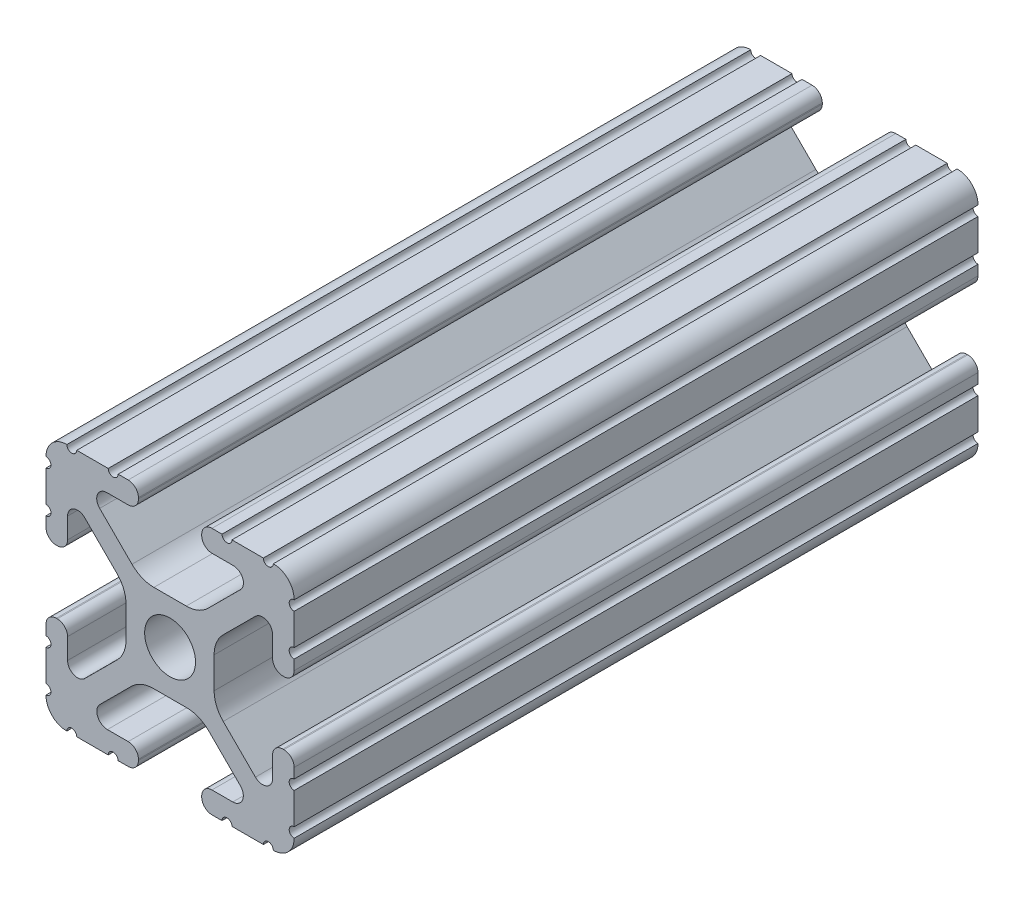
SolidWorks part; units mm, degrees
ref_plane "Front Plane" through (0, 0, 0) normal (0, 0, 1) x (1, 0, 0)
ref_plane "Top Plane" through (0, 0, 0) normal (0, 1, 0) x (1, 0, 0)
ref_plane "Right Plane" through (0, 0, 0) normal (1, 0, 0) x (0, 0, -1)
sketch "Sketch1" plane through (0, 0, 0) normal (0, 0, 1) x (1, 0, 0)
  line L88 (-7.1797, -8.6452) -> (-3.9523, -5.4237)
  line L89 (-1.7093, -4.4958) -> (1.7093, -4.4958)
  line L90 (3.9523, -5.4237) -> (7.1797, -8.6452)
  line L91 (6.4164, -10.4902) -> (4.2875, -10.4902)
  line L92 (3.2385, -11.5392) -> (3.2385, -11.651)
  line L93 (4.2875, -12.7) -> (5.3171, -12.7)
  line L94 (6.3331, -12.7) -> (9.5504, -12.7)
  line L95 (12.7, -9.5504) -> (12.7, -6.3331)
  line L96 (12.7, -5.3171) -> (12.7, -4.2875)
  line L97 (11.651, -3.2385) -> (11.5392, -3.2385)
  line L98 (10.4902, -4.2875) -> (10.4902, -6.4021)
  line L99 (8.7371, -7.1294) -> (5.441, -3.8408)
  line L100 (4.5085, -1.5932) -> (4.5085, 1.5932)
  line L101 (5.441, 3.8408) -> (8.7371, 7.1294)
  line L102 (10.4902, 6.4021) -> (10.4902, 4.2875)
  line L103 (11.5392, 3.2385) -> (11.651, 3.2385)
  line L104 (12.7, 4.2875) -> (12.7, 5.3171)
  line L105 (12.7, 6.3331) -> (12.7, 9.5504)
  line L106 (9.5504, 12.7) -> (6.3331, 12.7)
  line L107 (5.3171, 12.7) -> (4.2875, 12.7)
  line L108 (3.2385, 11.651) -> (3.2385, 11.5392)
  line L109 (4.2875, 10.4902) -> (6.4768, 10.4902)
  line L110 (7.207, 8.7244) -> (3.8983, 5.4232)
  line L111 (1.6558, 4.4958) -> (-1.6558, 4.4958)
  line L112 (-3.8983, 5.4232) -> (-7.207, 8.7244)
  line L113 (-6.4768, 10.4902) -> (-4.2875, 10.4902)
  line L114 (-3.2385, 11.5392) -> (-3.2385, 11.651)
  line L115 (-4.2875, 12.7) -> (-5.3171, 12.7)
  line L116 (-6.3331, 12.7) -> (-9.5504, 12.7)
  line L117 (-12.7, 9.5504) -> (-12.7, 6.3331)
  line L118 (-12.7, 5.3171) -> (-12.7, 4.2875)
  line L119 (-11.651, 3.2385) -> (-11.5392, 3.2385)
  line L120 (-10.4902, 4.2875) -> (-10.4902, 6.4021)
  line L121 (-8.7371, 7.1294) -> (-5.441, 3.8408)
  line L122 (-4.5085, 1.5932) -> (-4.5085, -1.5932)
  line L123 (-5.441, -3.8408) -> (-8.7371, -7.1294)
  line L124 (-10.4902, -6.4021) -> (-10.4902, -4.2875)
  line L125 (-11.5392, -3.2385) -> (-11.651, -3.2385)
  line L126 (-12.7, -4.2875) -> (-12.7, -5.3171)
  line L127 (-12.7, -6.3331) -> (-12.7, -9.5504)
  line L128 (-9.5504, -12.7) -> (-6.3331, -12.7)
  line L129 (-5.3171, -12.7) -> (-4.2875, -12.7)
  line L130 (-3.2385, -11.651) -> (-3.2385, -11.5392)
  line L131 (-4.2875, -10.4902) -> (-6.4164, -10.4902)
  circle A1 centre (0, 0) radius 2.6035
  arc A104 (-7.1797, -8.6452) -> (-6.4164, -10.4902) centre (-6.4164, -9.4098) ccw
  arc A105 (-1.7093, -4.4958) -> (-3.9523, -5.4237) centre (-1.7093, -7.6708) ccw
  arc A106 (3.9523, -5.4237) -> (1.7093, -4.4958) centre (1.7093, -7.6708) ccw
  arc A107 (6.4164, -10.4902) -> (7.1797, -8.6452) centre (6.4164, -9.4098) ccw
  arc A108 (4.2875, -10.4902) -> (3.2385, -11.5392) centre (4.2875, -11.5392) ccw
  arc A109 (3.2385, -11.651) -> (4.2875, -12.7) centre (4.2875, -11.651) ccw
  arc A110 (6.3331, -12.7) -> (5.3171, -12.7) centre (5.8251, -12.7) ccw
  arc A111 (10.5664, -12.6998) -> (9.5504, -12.7) centre (10.0584, -12.7) ccw
  arc A112 (10.5664, -12.6998) -> (12.6998, -10.5664) centre (10.5918, -10.5918) ccw
  arc A113 (12.7, -9.5504) -> (12.6998, -10.5664) centre (12.7, -10.0584) ccw
  arc A114 (12.7, -5.3171) -> (12.7, -6.3331) centre (12.7, -5.8251) ccw
  arc A115 (12.7, -4.2875) -> (11.651, -3.2385) centre (11.651, -4.2875) ccw
  arc A116 (11.5392, -3.2385) -> (10.4902, -4.2875) centre (11.5392, -4.2875) ccw
  arc A117 (8.7371, -7.1294) -> (10.4902, -6.4021) centre (9.4628, -6.4021) ccw
  arc A118 (4.5085, -1.5932) -> (5.441, -3.8408) centre (7.6835, -1.5932) ccw
  arc A119 (5.441, 3.8408) -> (4.5085, 1.5932) centre (7.6835, 1.5932) ccw
  arc A120 (10.4902, 6.4021) -> (8.7371, 7.1294) centre (9.4628, 6.4021) ccw
  arc A121 (10.4902, 4.2875) -> (11.5392, 3.2385) centre (11.5392, 4.2875) ccw
  arc A122 (11.651, 3.2385) -> (12.7, 4.2875) centre (11.651, 4.2875) ccw
  arc A123 (12.7, 6.3331) -> (12.7, 5.3171) centre (12.7, 5.8251) ccw
  arc A124 (12.6998, 10.5664) -> (12.7, 9.5504) centre (12.7, 10.0584) ccw
  arc A125 (12.6998, 10.5664) -> (10.5664, 12.6998) centre (10.5918, 10.5918) ccw
  arc A126 (9.5504, 12.7) -> (10.5664, 12.6998) centre (10.0584, 12.7) ccw
  arc A127 (5.3171, 12.7) -> (6.3331, 12.7) centre (5.8251, 12.7) ccw
  arc A128 (4.2875, 12.7) -> (3.2385, 11.651) centre (4.2875, 11.651) ccw
  arc A129 (3.2385, 11.5392) -> (4.2875, 10.4902) centre (4.2875, 11.5392) ccw
  arc A130 (7.207, 8.7244) -> (6.4768, 10.4902) centre (6.4768, 9.4563) ccw
  arc A131 (1.6558, 4.4958) -> (3.8983, 5.4232) centre (1.6558, 7.6708) ccw
  arc A132 (-3.8983, 5.4232) -> (-1.6558, 4.4958) centre (-1.6558, 7.6708) ccw
  arc A133 (-6.4768, 10.4902) -> (-7.207, 8.7244) centre (-6.4768, 9.4563) ccw
  arc A134 (-4.2875, 10.4902) -> (-3.2385, 11.5392) centre (-4.2875, 11.5392) ccw
  arc A135 (-3.2385, 11.651) -> (-4.2875, 12.7) centre (-4.2875, 11.651) ccw
  arc A136 (-6.3331, 12.7) -> (-5.3171, 12.7) centre (-5.8251, 12.7) ccw
  arc A137 (-10.5664, 12.6998) -> (-9.5504, 12.7) centre (-10.0584, 12.7) ccw
  arc A138 (-10.5664, 12.6998) -> (-12.6998, 10.5664) centre (-10.5918, 10.5918) ccw
  arc A139 (-12.7, 9.5504) -> (-12.6998, 10.5664) centre (-12.7, 10.0584) ccw
  arc A140 (-12.7, 5.3171) -> (-12.7, 6.3331) centre (-12.7, 5.8251) ccw
  arc A141 (-12.7, 4.2875) -> (-11.651, 3.2385) centre (-11.651, 4.2875) ccw
  arc A142 (-11.5392, 3.2385) -> (-10.4902, 4.2875) centre (-11.5392, 4.2875) ccw
  arc A143 (-8.7371, 7.1294) -> (-10.4902, 6.4021) centre (-9.4628, 6.4021) ccw
  arc A144 (-4.5085, 1.5932) -> (-5.441, 3.8408) centre (-7.6835, 1.5932) ccw
  arc A145 (-5.441, -3.8408) -> (-4.5085, -1.5932) centre (-7.6835, -1.5932) ccw
  arc A146 (-10.4902, -6.4021) -> (-8.7371, -7.1294) centre (-9.4628, -6.4021) ccw
  arc A147 (-10.4902, -4.2875) -> (-11.5392, -3.2385) centre (-11.5392, -4.2875) ccw
  arc A148 (-11.651, -3.2385) -> (-12.7, -4.2875) centre (-11.651, -4.2875) ccw
  arc A149 (-12.7, -6.3331) -> (-12.7, -5.3171) centre (-12.7, -5.8251) ccw
  arc A150 (-12.6998, -10.5664) -> (-12.7, -9.5504) centre (-12.7, -10.0584) ccw
  arc A151 (-12.6998, -10.5664) -> (-10.5664, -12.6998) centre (-10.5918, -10.5918) ccw
  arc A152 (-9.5504, -12.7) -> (-10.5664, -12.6998) centre (-10.0584, -12.7) ccw
  arc A153 (-5.3171, -12.7) -> (-6.3331, -12.7) centre (-5.8251, -12.7) ccw
  arc A154 (-4.2875, -12.7) -> (-3.2385, -11.651) centre (-4.2875, -11.651) ccw
  arc A155 (-3.2385, -11.5392) -> (-4.2875, -10.4902) centre (-4.2875, -11.5392) ccw
extrude "Boss-Extrude1" add sketch "Sketch1" along normal mid plane 70
